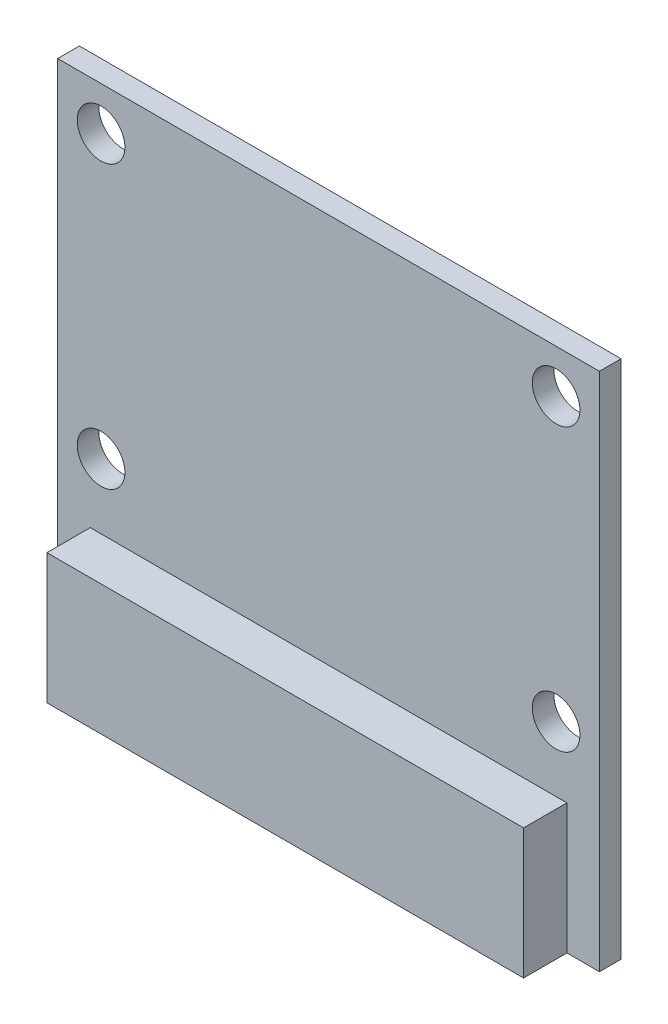
SolidWorks part; units mm, degrees
ref_plane "前视基准面" through (0, 0, 0) normal (0, 0, 1) x (1, 0, 0)
ref_plane "上视基准面" through (0, 0, 0) normal (0, 1, 0) x (1, 0, 0)
ref_plane "右视基准面" through (0, 0, 0) normal (1, 0, 0) x (0, 0, -1)
sketch "草图1" plane through (0, 0, 0) normal (0, 0, 1) x (1, 0, 0)
  line L0 (0, 12) -> (0, -12) construction
  line L1 (-12.5, 12) -> (12.5, 12)
  line L2 (-12.5, 12) -> (-12.5, -12)
  line L3 (-12.5, -12) -> (12.5, -12)
  line L4 (12.5, 12) -> (12.5, -12)
  line L5 (-12.5, 12) -> (12.5, -12) construction
  line L6 (-12.5, -12) -> (12.5, 12) construction
  circle A0 centre (-10.5, 10) radius 1.1
  circle A1 centre (-10.5, -3) radius 1.1
  circle A2 centre (10.5, -3) radius 1.1
  circle A3 centre (10.5, 10) radius 1.1
  point P0 (0, 0)
  dimension "D3" = 2.2
  dimension "D6" = 2.2
  dimension "D7" = 2
  dimension "D1" = 25
  dimension "D2" = 24
  dimension "D4" = 2
  dimension "D5" = 2
  dimension "D8" = 13
extrude "凸台-拉伸1" add sketch "草图1" along normal blind 1
sketch "草图2" plane through (0, 0, 1) normal (0, 0, 1) x (1, 0, 0)
  line L1 (-11, -12) -> (11, -12)
  line L2 (-11, -12) -> (-11, -6)
  line L3 (-11, -6) -> (11, -6)
  line L4 (12.5, -12) -> (12.5, 12)
  line L5 (12.5, 12) -> (-12.5, 12)
  line L6 (-12.5, 12) -> (-12.5, -12)
  line L7 (-12.5, -12) -> (12.5, -12)
  line L8 (12.5, -12) -> (12.5, 12)
  line L9 (12.5, 12) -> (-12.5, 12)
  line L10 (-12.5, 12) -> (-12.5, -12)
  line L11 (-12.5, -12) -> (12.5, -12)
  line L12 (11, -12) -> (11, -6)
  line M12 (-12.5, -12) -> (12.5, -12)
  dimension "D2" = 22
  dimension "D3" = 6
  dimension "D4" = 1.5
  dimension "D1" = 0
extrude "凸台-拉伸2" add sketch "草图2" along normal blind 2 contours L12 L3 L2 M12
sketch "草图3" plane through (0, 0, 0) normal (0, 0, -1) x (-1, 0, 0)
  line L0 (0, 12) -> (0, -12) construction
  line L1 (-4.5, 2) -> (4.5, 2)
  line L2 (-4.5, 2) -> (-4.5, -7)
  line L3 (-4.5, -7) -> (4.5, -7)
  line L4 (-12.5, 12) -> (-12.5, -12)
  line L5 (-12.5, -12) -> (12.5, -12)
  line L6 (12.5, -12) -> (12.5, 12)
  line L7 (12.5, 12) -> (-12.5, 12)
  line L8 (-12.5, 12) -> (-12.5, -12)
  line L9 (-12.5, -12) -> (12.5, -12)
  line L10 (12.5, -12) -> (12.5, 12)
  line L11 (12.5, 12) -> (-12.5, 12)
  line L12 (4.5, 2) -> (4.5, -7)
  line L13 (-4.5, 2) -> (4.5, -7) construction
  line L14 (-4.5, -7) -> (4.5, 2) construction
  point P2 (0, -2.5)
  point P11 (0, 0)
  dimension "D2" = 9
  dimension "D3" = 9
  dimension "D4" = 10
  dimension "D1" = 0
extrude "凸台-拉伸3" add sketch "草图3" along normal blind 2.5 contours L12 L1 L2 L3
sketch "草图4" plane through (0, 0, -2.5) normal (0, 0, -1) x (-1, 0, 0)
  line L0 (-4.5, 2) -> (4.5, -7) construction
  line L4 (4.5, -7) -> (4.5, 2)
  line L5 (4.5, 2) -> (-4.5, 2)
  line L6 (-4.5, 2) -> (-4.5, -7)
  line L7 (-4.5, -7) -> (4.5, -7)
  line L8 (4.5, -7) -> (4.5, 2)
  line L9 (4.5, 2) -> (-4.5, 2)
  line L10 (-4.5, 2) -> (-4.5, -7)
  line L11 (-4.5, -7) -> (4.5, -7)
  circle A0 centre (0, -2.5) radius 3.5
  dimension "D2" = 7
  dimension "D1" = 0
extrude "凸台-拉伸4" add sketch "草图4" along normal blind 1.5 contours A0
sketch "草图5" plane through (0, 0, 0) normal (0, 0, -1) x (-1, 0, 0)
  line L0 (0, 12) -> (0, -12) construction
  line L1 (-4.5, 2) -> (4.5, 2) construction
  line L2 (-3.5, 9) -> (3.5, 9)
  line L3 (-3.5, 9) -> (-3.5, 2)
  line L4 (-12.5, 12) -> (-12.5, -12)
  line L5 (-12.5, -12) -> (12.5, -12)
  line L6 (12.5, -12) -> (12.5, 12)
  line L7 (12.5, 12) -> (-12.5, 12)
  line L8 (-12.5, 12) -> (-12.5, -12)
  line L9 (-12.5, -12) -> (12.5, -12)
  line L10 (12.5, -12) -> (12.5, 12)
  line L11 (12.5, 12) -> (-12.5, 12)
  line L12 (-3.5, 2) -> (3.5, 2)
  line L13 (3.5, 9) -> (3.5, 2)
  line L14 (-3.5, 9) -> (3.5, 2) construction
  line L15 (-3.5, 2) -> (3.5, 9) construction
  point P6 (0, 5.5)
  dimension "D2" = 7
  dimension "D3" = 7
  dimension "D1" = 0
extrude "凸台-拉伸5" add sketch "草图5" along normal blind 1 contours L13 L12 L3 L2
